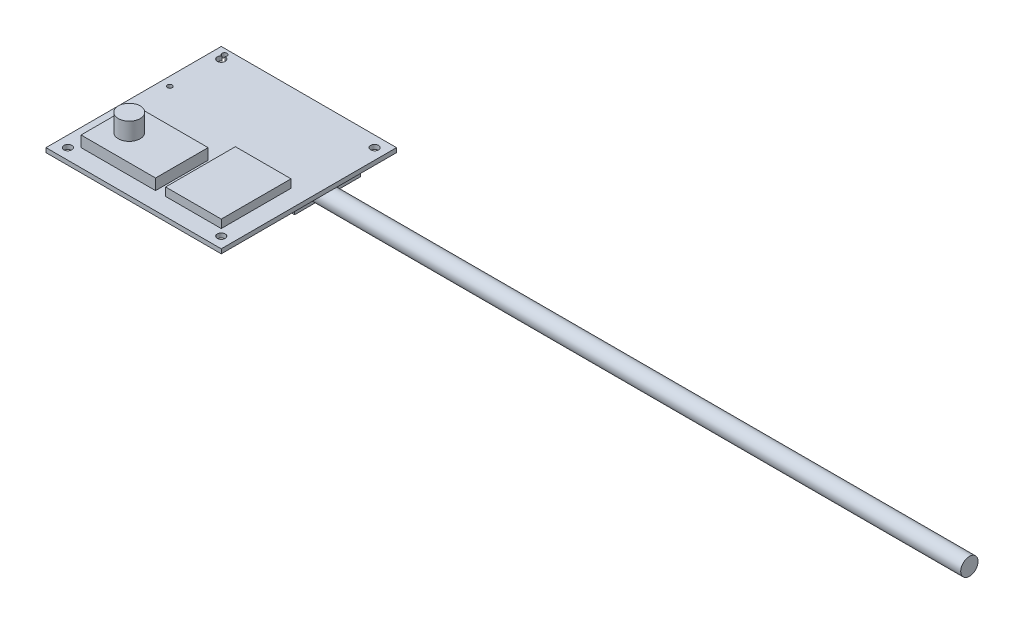
SolidWorks part; units mm, degrees
ref_plane "Front Plane" through (0, 0, 0) normal (0, 0, 1) x (1, 0, 0)
ref_plane "Top Plane" through (0, 0, 0) normal (0, 1, 0) x (1, 0, 0)
ref_plane "Right Plane" through (0, 0, 0) normal (1, 0, 0) x (0, 0, -1)
sketch "Sketch1" plane through (0, 0, 0) normal (0, 1, 0) x (1, 0, 0)
  line L1 (0, 0) -> (80, 0)
  line L2 (0, 0) -> (0, 80)
  line L3 (0, 80) -> (80, 80)
  line L4 (80, 0) -> (80, 80)
  dimension "D1" = 80
  dimension "D2" = 80
extrude "PCB" add sketch "Sketch1" along normal blind 2
sketch "Sketch2" plane through (0, 2, 0) normal (0, 1, 0) x (1, 0, 0)
  line L0 (80, 80) -> (0, 80) construction
  line L1 (0, 80) -> (0, 0) construction
  circle A0 centre (5, 75) radius 1.8
  dimension "D1" = 3.6
  dimension "D2" = 5
  dimension "D3" = 5
extrude "Attachment Holes" cut sketch "Sketch2" against normal through all
pattern_linear "LPattern1" count 2 spacing 70 along (1, 0, 0) count 2 spacing 70 along (0, 0, 1) of "Attachment Holes"
sketch "Sketch3" plane through (0, 0, 0) normal (0, 1, 0) x (1, 0, 0)
  line L0 (80, 80) -> (0, 80) construction
  line L1 (11.5, 75) -> (68.5, 75)
  line L2 (11.5, 75) -> (11.5, 45)
  line L3 (11.5, 45) -> (68.5, 45)
  line L4 (68.5, 75) -> (68.5, 45)
  line L5 (0, 80) -> (0, 0) construction
  dimension "D1" = 30
  dimension "D2" = 57
  dimension "D3" = 5
  dimension "D4" = 11.5
extrude "Comms Chip" add sketch "Sketch3" against normal blind 12.8
sketch "Sketch4" plane through (0, -12.8, 0) normal (0, -1, 0) x (-1, 0, 0)
  line L0 (-68.5, 75) -> (-11.5, 75) construction
  line L1 (-11.5, 75) -> (-11.5, 45) construction
  circle A0 centre (-4, 77.5) radius 1.115
  dimension "D1" = 2.23
  dimension "D2" = 2.5
  dimension "D3" = 7.5
extrude "Comm chip attachment" cut sketch "Sketch4" against normal through all
pattern_linear "LPattern2" count 2 spacing 25 along (0, 0, 1) of "Comm chip attachment"
sketch "Sketch5" plane through (0, 2, 0) normal (0, 1, 0) x (1, 0, 0)
  line L0 (0, 80) -> (0, 0) construction
  line L1 (8, 32) -> (42, 32)
  line L2 (8, 32) -> (8, 8)
  line L3 (8, 8) -> (42, 8)
  line L4 (42, 32) -> (42, 8)
  line L5 (0, 0) -> (80, 0) construction
  dimension "D1" = 34
  dimension "D2" = 24
  dimension "D3" = 8
  dimension "D4" = 8
extrude "ArducamMini" add sketch "Sketch5" along normal blind 5
sketch "Sketch8" plane through (0, 7, 0) normal (0, 1, 0) x (1, 0, 0)
  line L0 (42, 32) -> (8, 32) construction
  line L1 (8, 32) -> (8, 8) construction
  circle A0 centre (18, 20) radius 5
  point P6 (16.5339, 15.9501)
  dimension "D3" = 10
  dimension "D1" = 12
  dimension "D2" = 10
extrude "Lens, approximate" add sketch "Sketch8" along normal blind 8
sketch "Sketch6" plane through (0, 2, 0) normal (0, 1, 0) x (1, 0, 0)
  line L0 (0, 0) -> (80, 0) construction
  line L1 (46.6, 39.85) -> (72, 39.85)
  line L2 (46.6, 39.85) -> (46.6, 8)
  line L3 (46.6, 8) -> (72, 8)
  line L4 (72, 39.85) -> (72, 8)
  line L5 (80, 0) -> (80, 80) construction
  dimension "D1" = 31.85
  dimension "D2" = 25.4
  dimension "D3" = 8
  dimension "D4" = 8
extrude "SD Card" add sketch "Sketch6" along normal blind 3.75
sketch "Sketch7" plane through (68.5, -53.7, 0) normal (-1, 0, 0) x (0, 1, 0)
  line L0 (40.9, 45) -> (40.9, 75) construction
  line L2 (40.9, 45) -> (53.7, 45) construction
  circle A0 centre (47.9, 53) radius 3.95
  dimension "D1" = 7.9
  dimension "D2" = 7
  dimension "D3" = 8
extrude "Antenna" add sketch "Sketch7" against normal blind 300
